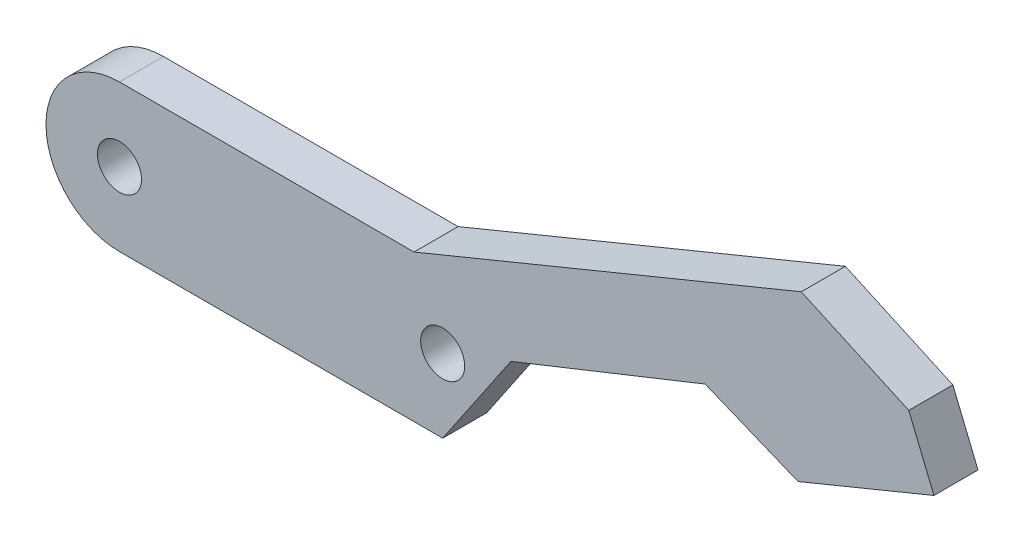
SolidWorks part; units mm, degrees
ref_plane "前视基准面" through (0, 0, 0) normal (0, 0, 1) x (1, 0, 0)
ref_plane "上视基准面" through (0, 0, 0) normal (0, 1, 0) x (1, 0, 0)
ref_plane "右视基准面" through (0, 0, 0) normal (1, 0, 0) x (0, 0, -1)
other "Configuration Table"
sketch "草图1" plane through (0, 0, 0) normal (0, 0, 1) x (1, 0, 0)
  line L0 (0, 0) -> (22, 0) construction
  line L1 (0, 5) -> (22, 5)
  line L2 (0, -5) -> (22, -5)
  line L3 (55.4373, 8.3426) -> (23.9914, -4.5863) construction
  line L4 (55.4373, 8.3426) -> (51.4959, 17.929) construction
  line L5 (23.9914, -4.5863) -> (20.05, 5) construction
  line L6 (51.4959, 17.929) -> (20.05, 5) construction
  line L7 (20.05, 5) -> (46.409, 15.8375)
  line L8 (46.409, 15.8375) -> (53.7261, 12.5046)
  line L9 (53.7261, 12.5046) -> (55.4373, 8.3426)
  line L10 (55.4373, 8.3426) -> (46.1885, 4.54)
  line L11 (46.1885, 4.54) -> (39.8718, 7.1258)
  line L12 (39.8718, 7.1258) -> (26.6444, 1.8518)
  line L13 (22, -5) -> (26.6444, 1.8518)
  arc A0 (0, 5) -> (0, -5) centre (0, 0) ccw
  arc A1 (22, -5) -> (22, 5) centre (22, 0) ccw
  circle A2 centre (22, 0) radius 1.5
  circle A3 centre (0, 0) radius 1.5
  point P3 (11, 0)
  dimension "D3" = 5
  dimension "D11" = 3
  dimension "D1" = 157.65
  dimension "D2" = 1.95
  dimension "D4" = 22
  dimension "D5" = 34
  dimension "D6" = 14.24
  dimension "D7" = 10
  dimension "D8" = 4.5
  dimension "D9" = 5.5
  dimension "D10" = 136
extrude "凸台-拉伸1" add sketch "草图1" along normal blind 3 contours A1 L1 A0 L2 A3 A2 | A1 L12 L11 L10 L9 L8 L7 L1
